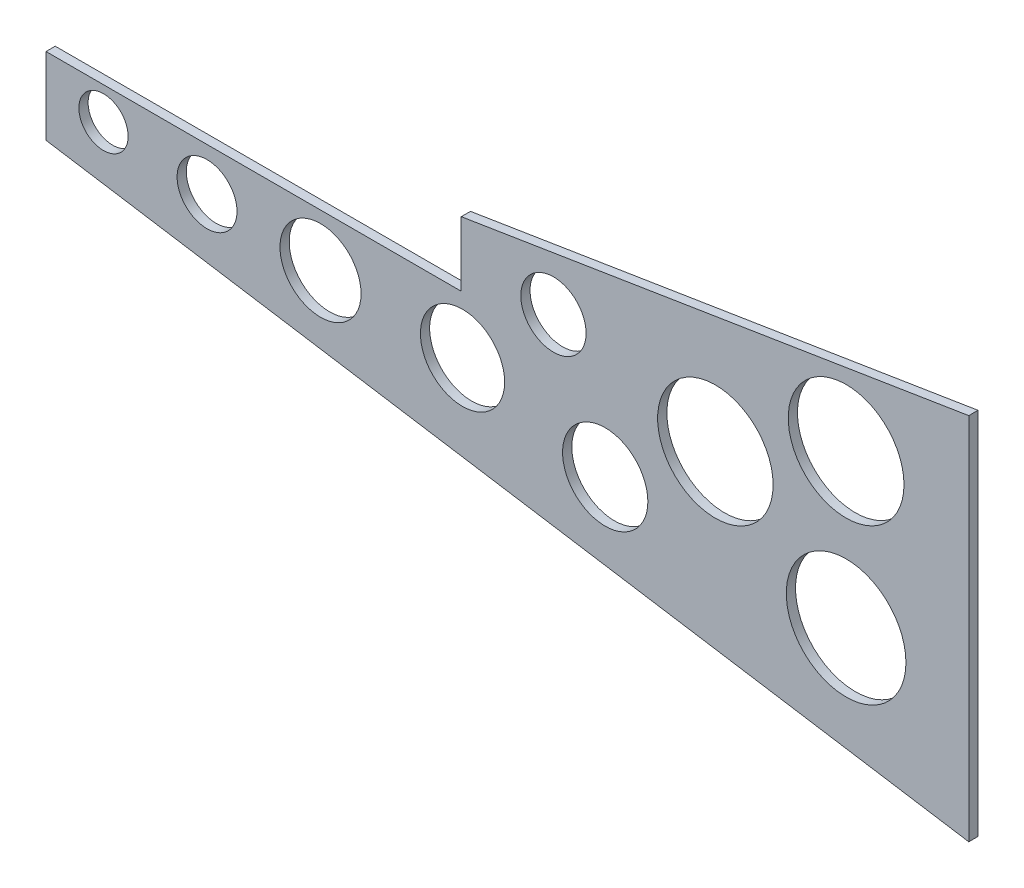
SolidWorks part; units mm, degrees
ref_plane "Front Plane" through (0, 0, 0) normal (0, 0, 1) x (1, 0, 0)
ref_plane "Top Plane" through (0, 0, 0) normal (0, 1, 0) x (1, 0, 0)
ref_plane "Right Plane" through (0, 0, 0) normal (1, 0, 0) x (0, 0, -1)
sketch "Sketch1" plane through (0, 0, 0) normal (0, 0, 1) x (1, 0, 0)
  line L0 (150, 56.604) -> (150, -63.396)
  line L1 (150, -63.396) -> (-150, -15.8807)
  line L2 (-150, -15.8807) -> (-150, 9.1193)
  line L3 (-150, 9.1193) -> (-15, 9.1193)
  line L4 (-15, 9.1193) -> (-15, 30.1193)
  line L5 (-15, 30.1193) -> (150, 56.604)
  line L6 (0, 0) -> (0, -39.6384) construction
  point P9 (0, -39.6384)
  dimension "D1" = 120
  dimension "D2" = 25
  dimension "D3" = 135
  dimension "D4" = 300
extrude "Boss-Extrude1" add sketch "Sketch1" along normal blind 3
sketch "Sketch2" plane through (0, 0, 3) normal (0, 0, 1) x (1, 0, 0)
  circle A0 centre (-131.3064, -1.4189) radius 8.0062
  circle A1 centre (-97.6488, -4.871) radius 9.7353
  circle A2 centre (-60.7549, -7.8915) radius 13.1822
  circle A3 centre (-14.5835, -9.4251) radius 13.6914
  circle A4 centre (110.1223, -23.1165) radius 19.4508
  circle A5 centre (110.1223, 26.6291) radius 18.8139
  circle A6 centre (67.6187, 5.2907) radius 18.7706
  circle A7 centre (31.8036, -19.758) radius 13.8638
  circle A8 centre (14.9748, 17.5675) radius 10.6137
extrude "Cut-Extrude1" cut sketch "Sketch2" against normal blind 3
